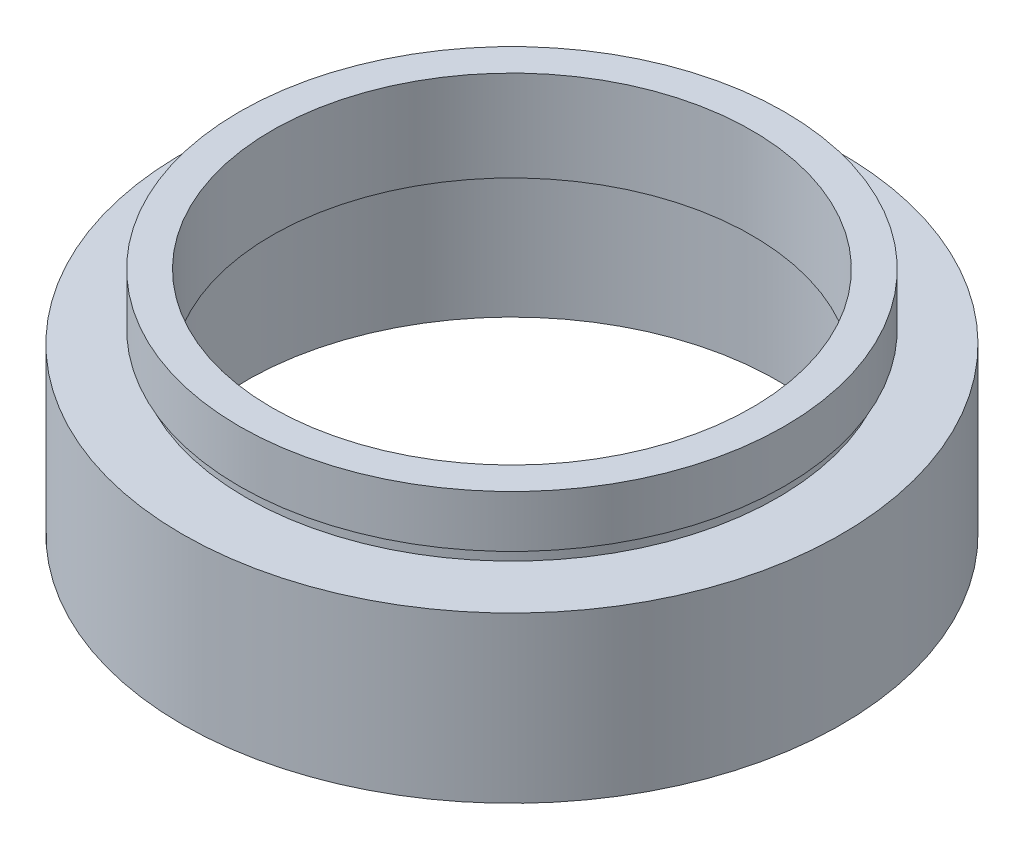
SolidWorks part; units mm, degrees
ref_plane "前视基准面" through (0, 0, 0) normal (0, 0, 1) x (1, 0, 0)
ref_plane "上视基准面" through (0, 0, 0) normal (0, 1, 0) x (1, 0, 0)
ref_plane "右视基准面" through (0, 0, 0) normal (1, 0, 0) x (0, 0, -1)
sketch "草图1" plane through (0, 0, 0) normal (0, 0, 1) x (1, 0, 0)
  line L0 (0, 161.3762) -> (0, 0) construction
  line L1 (141.7365, 0) -> (-131.7984, 0) construction
  line L2 (18.5, 17.7) -> (21, 17.7)
  line L3 (21, 17.7) -> (21, 13.7)
  line L4 (21, 13.7) -> (20.5, 13.7)
  line L5 (20.5, 13.7) -> (20.5, 12.7)
  line L6 (20.5, 12.7) -> (25.4, 12.7)
  line L7 (25.4, 12.7) -> (25.4, 0)
  line L8 (25.4, 0) -> (20.5, 0)
  line L9 (20.5, 0) -> (20.5, 9.7)
  line L10 (20.5, 9.7) -> (21.1, 9.7)
  line L11 (21.1, 9.7) -> (21.1, 10.7)
  line L12 (21.1, 10.7) -> (18.5, 10.7)
  line L13 (18.5, 10.7) -> (18.5, 17.7)
  dimension "D1" = 18.5
  dimension "D2" = 21
  dimension "D3" = 1
  dimension "D4" = 1
  dimension "D5" = 20.5
  dimension "D6" = 21.1
  dimension "D7" = 20.5
  dimension "D8" = 5
  dimension "D9" = 7
  dimension "D10" = 12.7
  dimension "D11" = 25.4
revolve "旋转1" add sketch "草图1" angle 360 about L0
cosmetic thread "装饰螺纹线1"
cosmetic thread "装饰螺纹线2"
cosmetic thread "装饰螺纹线3"
